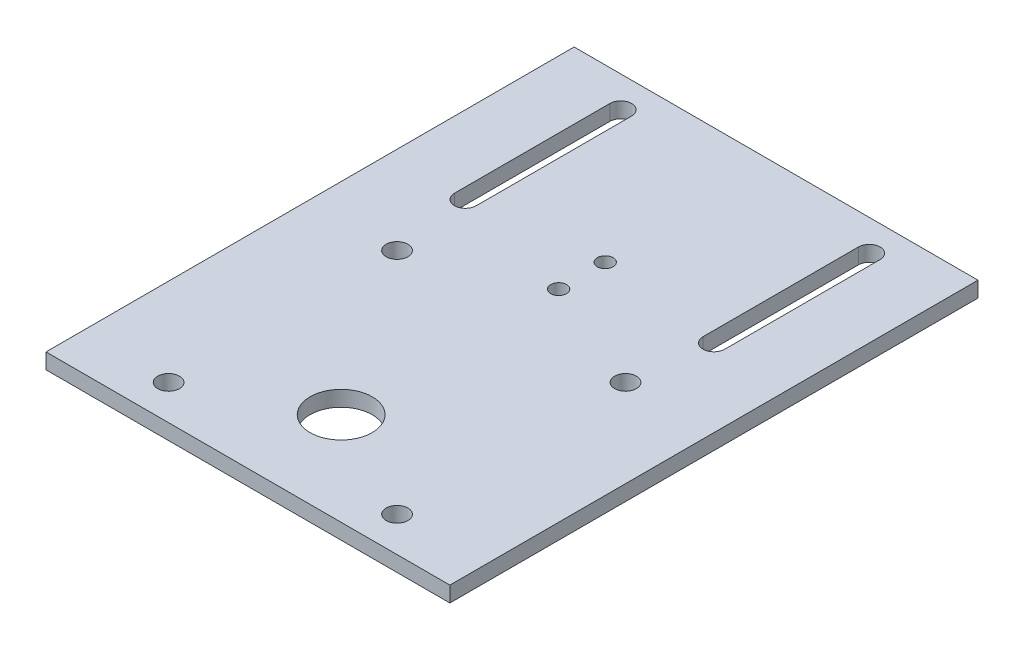
SolidWorks part; units mm, degrees
ref_plane "前视基准面" through (0, 0, 0) normal (0, 0, 1) x (1, 0, 0)
ref_plane "上视基准面" through (0, 0, 0) normal (0, 1, 0) x (1, 0, 0)
ref_plane "右视基准面" through (0, 0, 0) normal (1, 0, 0) x (0, 0, -1)
sketch "草图3" plane through (0, 0, 0) normal (0, 1, 0) x (1, 0, 0)
  line L1 (-65, -85) -> (65, -85)
  line L2 (-65, -85) -> (-65, 85)
  line L3 (-65, 85) -> (65, 85)
  line L4 (65, -85) -> (65, 85)
  line L5 (-65, -85) -> (65, 85) construction
  line L6 (-65, 85) -> (65, -85) construction
  point P0 (0, 0)
  dimension "D1" = 130
  dimension "D2" = 170
extrude "凸台-拉伸1" add sketch "草图3" along normal blind 5 contours L3 L4 L1 L2
sketch "草图4" plane through (0, 0, 0) normal (0, -1, 0) x (1, 0, 0)
  line L0 (-65, 85) -> (65, 85) construction
  line L1 (65, 85) -> (65, -85) construction
  circle A0 centre (0, 55) radius 10
  dimension "D2" = 20
  dimension "D1" = 30
  dimension "D3" = 65
extrude "切除-拉伸1" cut sketch "草图4" against normal blind 10
sketch "草图5" plane through (0, 0, 0) normal (0, -1, 0) x (1, 0, 0)
  line L0 (0, -22.3188) -> (0, -77.4048) construction
  line L1 (36.7696, 0.2304) -> (-36.7696, 0.2304) construction
  line L2 (36.7696, 0.2304) -> (36.7696, 73.7696) construction
  line L3 (36.7696, 73.7696) -> (-36.7696, 73.7696) construction
  line L4 (-36.7696, 0.2304) -> (-36.7696, 73.7696) construction
  line L5 (36.7696, 0.2304) -> (-36.7696, 73.7696) construction
  line L6 (36.7696, 73.7696) -> (-36.7696, 0.2304) construction
  line L7 (40, -75) -> (40, -25) construction
  line L8 (36.5, -75) -> (36.5, -25)
  line L9 (43.5, -75) -> (43.5, -25)
  line L10 (-40, -75) -> (-40, -25) construction
  line L11 (-36.5, -75) -> (-36.5, -25)
  line L12 (-43.5, -75) -> (-43.5, -25)
  line L13 (-65, -85) -> (65, -85) construction
  line L14 (-65, 85) -> (65, 85) construction
  circle A0 centre (36.7696, 0.2304) radius 3.5
  circle A1 centre (-36.7696, 0.2304) radius 3.5
  circle A2 centre (-36.7696, 73.7696) radius 3.5
  circle A3 centre (36.7696, 73.7696) radius 3.5
  circle A6 centre (0, -30) radius 2.55
  circle A7 centre (0, -15) radius 2.55
  arc A8 (36.5, -75) -> (43.5, -75) centre (40, -75) ccw
  arc A9 (43.5, -25) -> (36.5, -25) centre (40, -25) ccw
  arc A10 (-36.5, -75) -> (-43.5, -75) centre (-40, -75) cw
  arc A11 (-43.5, -25) -> (-36.5, -25) centre (-40, -25) cw
  circle A12 centre (0, 37) radius 52 construction
  circle A13 centre (0, 55) radius 10 construction
  point P0 (0, 37)
  point P12 (40, -50)
  point P26 (-40, -50)
  dimension "D3" = 7
  dimension "D4" = 7
  dimension "D7" = 5.1
  dimension "D12" = 104
  dimension "D2" = 18
  dimension "D5" = 50
  dimension "D6" = 15
  dimension "D8" = 80
  dimension "D9" = 10
  dimension "D11" = 100
extrude "切除-拉伸2" cut sketch "草图5" against normal blind 10
